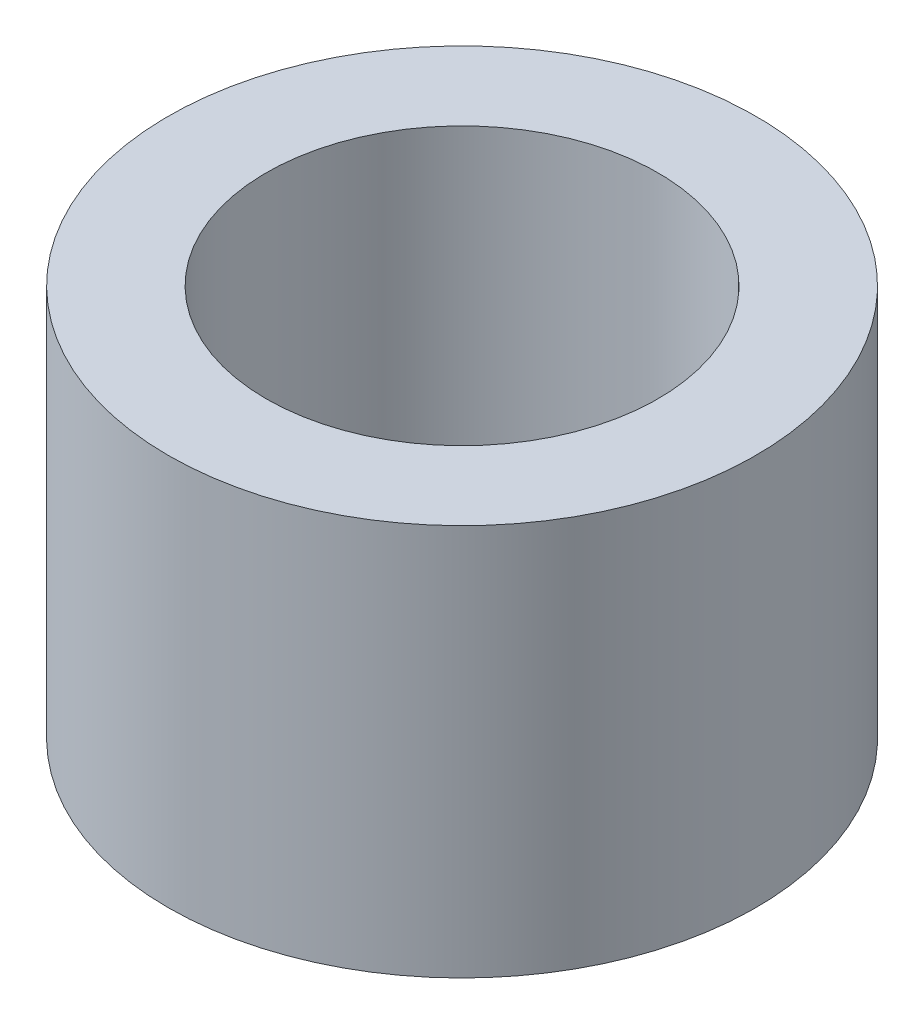
SolidWorks part; units mm, degrees
ref_plane "Front Plane" through (0, 0, 0) normal (0, 0, 1) x (1, 0, 0)
ref_plane "Top Plane" through (0, 0, 0) normal (0, 1, 0) x (1, 0, 0)
ref_plane "Right Plane" through (0, 0, 0) normal (1, 0, 0) x (0, 0, -1)
sketch "Sketch1" plane through (0, 0, 0) normal (0, 1, 0) x (1, 0, 0)
  circle A0 centre (0, 0) radius 3.175
  circle A1 centre (0, 0) radius 4.7625
  dimension "D1" = 6.35
  dimension "D2" = 9.525
extrude "Boss-Extrude1" add sketch "Sketch1" along normal blind 6.35
